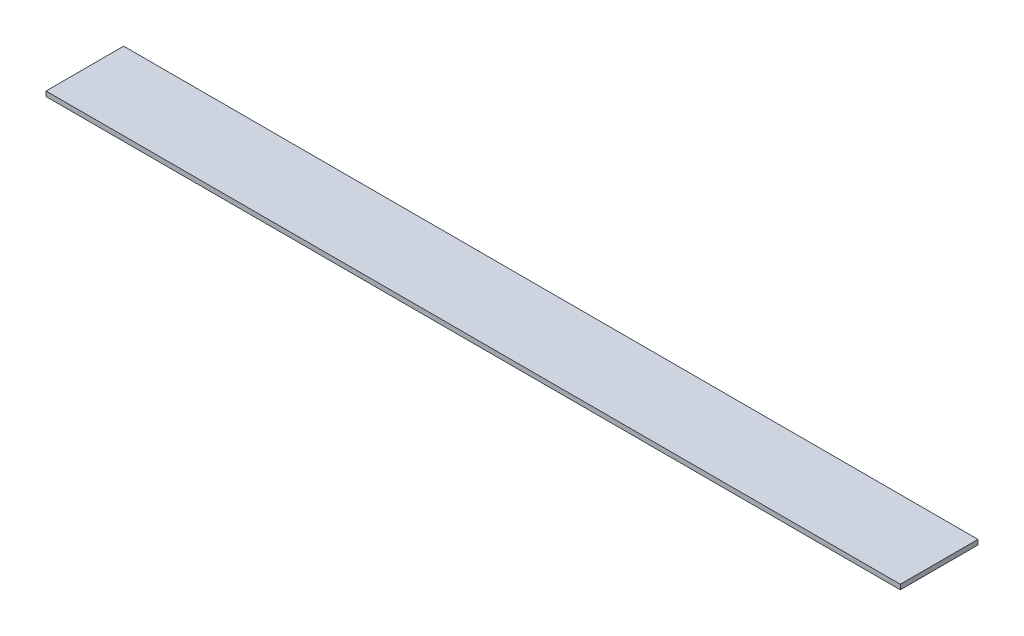
SolidWorks part; units mm, degrees
material "Nylon 6/10"
ref_plane "Front Plane" through (0, 0, 0) normal (0, 0, 1) x (1, 0, 0)
ref_plane "Top Plane" through (0, 0, 0) normal (0, 1, 0) x (1, 0, 0)
ref_plane "Right Plane" through (0, 0, 0) normal (1, 0, 0) x (0, 0, -1)
sketch "Sketch1" plane through (0, -80.2624, 0) normal (0, -1, 0) x (1, 0, 0)
  line L2 (0, 0) -> (558.8, 0)
  line L3 (0, 0) -> (0, 50.8)
  line L4 (0, 50.8) -> (558.8, 50.8)
  line L5 (558.8, 0) -> (558.8, 50.8)
  dimension "D2" = 558.8
  dimension "D1" = 50.8
extrude "Boss-Extrude1" add sketch "Sketch1" along normal blind 3.175
